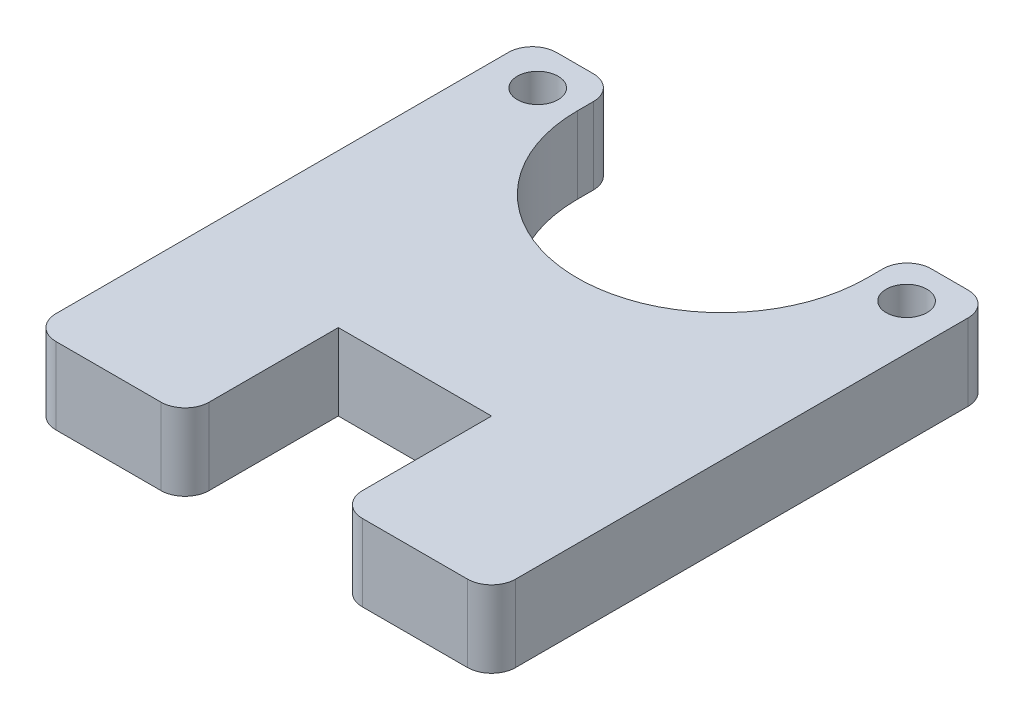
SolidWorks part; units mm, degrees
material "Beech"
ref_plane "Front Plane" through (0, 0, 0) normal (0, 0, 1) x (1, 0, 0)
ref_plane "Top Plane" through (0, 0, 0) normal (0, 1, 0) x (1, 0, 0)
ref_plane "Right Plane" through (0, 0, 0) normal (1, 0, 0) x (0, 0, -1)
sketch "Sketch1" plane through (0, 0, 0) normal (0, 1, 0) x (1, 0, 0)
  line L0 (0, 0) -> (0, 6)
  line L1 (0, 0) -> (19.05, 0)
  line L2 (0, 6) -> (19.05, 6)
  line L3 (19.05, 0) -> (19.05, 6)
  line L4 (0, 6) -> (0, 14.3936)
  line L5 (0, 6) -> (3.525, 6)
  line L6 (0, 14.3936) -> (3.525, 14.3936)
  line L7 (3.525, 6) -> (3.525, 14.3936)
  line L8 (19.05, 6) -> (19.05, 14.3936)
  line L9 (19.05, 6) -> (15.525, 6)
  line L10 (19.05, 14.3936) -> (15.525, 14.3936)
  line L11 (15.525, 6) -> (15.525, 14.3936)
  line L12 (0, 0) -> (6.35, 0)
  line L13 (0, 0) -> (0, -6.35)
  line L14 (6.35, 0) -> (6.35, -6.35)
  line L15 (0, -6.35) -> (6.35, -6.35)
  line L16 (19.05, 0) -> (12.7, 0)
  line L17 (19.05, 0) -> (19.05, -6.35)
  line L18 (12.7, 0) -> (12.7, -6.35)
  line L19 (19.05, -6.35) -> (12.7, -6.35)
  arc A0 (3.525, 12.7286) -> (15.525, 12.7286) centre (9.525, 12.7286) ccw
  circle A1 centre (17.1675, 12.7286) radius 0.845
  circle A2 centre (1.8825, 12.7286) radius 0.845
  point P8 (9.525, 6)
  dimension "D6" = 1.69
  dimension "D1" = 6
  dimension "D2" = 6.35
  dimension "D3" = 6.7286
  dimension "D4" = 6
  dimension "D5" = 1.665
  dimension "D7" = 1.6425
  dimension "D9" = 6.35
  dimension "D10" = 6.35
  dimension "D11" = 6.35
  dimension "D12" = 6.35
  dimension "D13" = 1.6425
extrude "Mount Body" add sketch "Sketch1" along normal blind 3.175 contours L2 L7 L6 L4 A2 | A0 L7 L2 L11 | L11 L2 L8 L10 A1 | L1 L3 L2 L0 | L13 L15 L14 L1 | L19 L17 L1 L18
fillet "Fillet3" radius 1 8 edges at (19.05, 1.5875, 6.35) (12.7, 1.5875, 6.35) (6.35, 1.5875, 6.35) (0, 1.5875, 6.35) (19.05, 1.5875, -14.3936) (15.525, 1.5875, -14.3936) (3.525, 1.5875, -14.3936) (0, 1.5875, -14.3936)
equation "\"vigorwidth\"= 0.472441in"
equation "\"vigorflangewidth\"= 0.731102in"
equation "\"vigorflangelength\"= 0.131102in"
equation "\"vigorscrewsize\"= 0.066535in"
equation "\"vigorholeoffsetwid\"= 0.0646653in"
equation "\"vigorholeoffsetlen\"= 0.065551in"
equation "\"vigorflangedepth\"= 0.0901575in"
equation "\"vigordiscdepth\"= 0.0492126in"
equation "\"vigormotordepth\"= 1.12362in"
equation "\"vigortipdepth\"= 0.259055in"
equation "\"vigoraxlewidth\"= 0.173622in"
equation "\"vigorcutlen\"= 0.0480315in"
equation "\"vigoraxledepth\"= 0.159055in"
equation "\"D4@Sketch1\"=\"vigorwidth\"/2"
equation "\"TriggerRackOffset\"=6mm"
equation "\"D1@Sketch1\" = \"TriggerRackOffset\""
equation "\"TriggerSlotSizeInt\"=.25in"
equation "\"D10@Sketch1\" = \"TriggerSlotSizeInt\""
equation "\"D9@Sketch1\" = \"TriggerSlotSizeInt\""
equation "\"MotorMountLegLength\"=.25in"
equation "\"D11@Sketch1\"=\"MotorMountLegLength\""
equation "\"D12@Sketch1\"=\"MotorMountLegLength\""
equation "\"GearOffset\"=.264907in"
equation "\"D3@Sketch1\"=\"GearOffset\""
equation "\"D7@Sketch1\"=\"vigorholeoffsetwid\""
equation "\"D13@Sketch1\"=\"vigorholeoffsetwid\""
equation "\"D5@Sketch1\"=\"vigorflangelength\"/2"
equation "\"TriggerSlotSpacing\"=.25in"
equation "\"D2@Sketch1\" = \"TriggerSlotSpacing\""
equation "\"D6@Sketch1\"=\"vigorscrewsize\""
equation "\"CageLeftBottomEdge\"=22.11mm"
equation "\"CageLeftTopEdge\"=22.11mm"
equation "\"CageRightBottomEdge\"=21.63mm"
equation "\"CageRightTopEdge\"=21.63mm"
equation "\"CageHeight\"=86.04mm"
equation "\"CageLength\"=73.76mm"
equation "\"CageTopScrewClearance\"=10mm"
equation "\"CageBottomScrewClearance\"=25mm"
equation "\"CageLeftTopDepth\"= 11.65mm"
equation "\"CageLeftBottomDepth\"=11.11mm"
equation "\"CageLeftTopHeight\"=8.56175mm"
equation "\"CageLeftBottomHeight\"=16mm"
equation "\"CageRightTopDepth\"= 11.05mm"
equation "\"CageRightBottomDepth\"=10.58mm"
equation "\"CageRightTopHeight\"=9.6mm"
equation "\"CageRightBottomHeight\"=15.49mm"
equation "\"CageLeftTopChannelDepth\"=2.41908mm"
equation "\"CageLeftBottomChannelDepth\"=2.588mm"
equation "\"CageLeftChannelHeight\"=11.7mm"
equation "\"CageRightTopChannelDepth\"=2.32mm"
equation "\"CageRightBottomChannelDepth\"=2.318mm"
equation "\"CageRightChannelHeight\"=10mm"
equation "\"CageChanRelHeight\"=23.99mm"
equation "\"CageChanRelDepth\"=5.492mm"
equation "\"CageChamberRadius\"=16.261mm"
equation "\"CageScrewDiameter\"=4.8mm"
equation "\"CageSetScrewDiameter\"=3.5mm"
equation "\"CageAxleRadius\"=6.639mm"
equation "\"CageAxleKeyHeight\"=1.619mm"
equation "\"CageAxleKeyWidth\"=2.662mm"
equation "\"CageHoseWindowWidth\"=16.29mm"
equation "\"CageHoseWindowHeight\"=26.5mm"
equation "\"CageHoseWindow-Edge\"=8.89mm"
equation "\"CageScrew-VerticalEdge\"=5.0mm"
equation "\"CageScrew-HorizontalEdge\"=7.5mm"
equation "\"CageScrew-HoseCornerScrewEdge\"=4.45mm"
equation "\"CageAxle-BottomEdge\"=56.05mm"
equation "\"CageAxle-FrontEdge\"=46.03mm"
equation "\"CageBackSetScrew-Axle\"=40mm"
equation "\"CageFrontSetScrew-Axle\"=22mm"
equation "\"CageVelocityWindow-BackEdge\"=34.8mm"
equation "\"CageVelocityWindow-BottomEdge\"=27.55mm"
equation "\"CageVelocityWindowHeight\"=22.29mm"
equation "\"CageVelocityWindowWidth\"=12.61mm"
equation "\"TriggerSlot-BottomEdge\"=6.35mm"
equation "\"TriggerSlot-FrontEdge\"=15mm"
equation "\"TriggerSlotSize\"=6.7mm"
equation "\"TriggerMiniSlotWidth\"=3.5mm"
equation "\"TriggerRackWidth\"=6.5mm"
equation "\"gearhubintdiam\"=30mm"
equation "\"gearhubintwid\"=12.21mm"
equation "\"pandiscradius\"=14in"
equation "\"towermaterialwidth\"=.25in"
equation "\"towerslotlength\"=.5in"
equation "\"towermarkerspace\"=5in"
equation "\"towerslothorizoffset\"=1in"
equation "\"towerslothorizspacing\"=2in"
equation "\"towerslotvertoffset\"=3in"
equation "\"towerslotvertspacing\"=1in"
equation "\"towerheight\"=12in"
equation "\"towerupslot\"=1in"
equation "\"toweraxle\"=.5in"
equation "\"towerspeedwidth\"=2in"
equation "\"towerspeedheight\"=8in"
equation "\"towerspeedgap\"=2in"
equation "\"stepperouterrad\"=10mm"
equation "\"stepperscrewsize\"=3.45mm"
equation "\"stepperscrewc2c\"=49.5mm"
equation "\"stepperdepthoffset\"=24mm"
equation "\"stepperhorizoffset\"=22.91mm"
equation "\"stepperaxleflat\"=.037in"
equation "\"stepperaxlerad\"=0.11811024in"
equation "\"shaftslotOD\"=18.8mm"
equation "\"shaftslotID\"=13.28mm"
equation "\"shaftkeywidth\"=2.67mm"
equation "\"shaftkeydepth\"=1.8mm"
equation "\"shaftcollartotaldepth\"=9.71mm"
equation "\"shaftsquaredepth\"=6mm"
equation "\"shaftsetscrewsize\"=3.5mm"
equation "\"shaftkeytightdepth\"=1.85mm"
equation "\"shaftslottightID\"=12.78mm"
equation "\"shaftsetscrewoffset\"=9mm"
equation "\"cagecollartotaldepth\"=20mm"
equation "\"cagecollartotalwidth\"=35mm"
equation "\"cagecollarbasedepth\"=4mm"
equation "\"ajaxaxlesize\"=3.87mm"
equation "\"ajaxinnercut\"=2.3mm"
equation "\"ajaxwidth\"=6.1mm"
equation "\"ajaxdiametral\"=25.8854"
equation "\"ajaxcutoutdepth\"=2.3mm"
equation "\"ajax4020gap\"=29.5mm"
equation "\"ajax4010gap\"=24.5mm"
equation "\"ajax20hubbuffer\"=6.1mm"
equation "\"ajax20hubholeoffset\"=.19685in"
equation "\"ajax20hubholesize\"=.059055in"
equation "\"ajax20cutoutint\"=13.4mm"
equation "\"ajax40hubholesize\"=7.21mm"
equation "\"ajax40hubholeoffset\"=10mm"
equation "\"ajax40hubbuffer\"=8.9mm"
equation "\"ajax40cutoutint\"=32.6mm"
equation "\"bearingpandiscrad\"=6.8in"
equation "\"bearingpandiscang\"=48.75deg"
equation "\"bearingclearholedist\"=4.7345in"
equation "\"bearingclearholesize\"=.5in"
equation "\"bearingclearholeang\"=22.5deg"
equation "\"bearingmountholedist\"=4.25in"
equation "\"bearingwirehole\"=1.5in"
equation "\"no6diam\"=.146in"
equation "\"shortconangle\"=20deg"
equation "\"shortconlen\"=.875in"
equation "\"longconlen\"=1.25in"
equation "\"longconangle\"=15deg"
